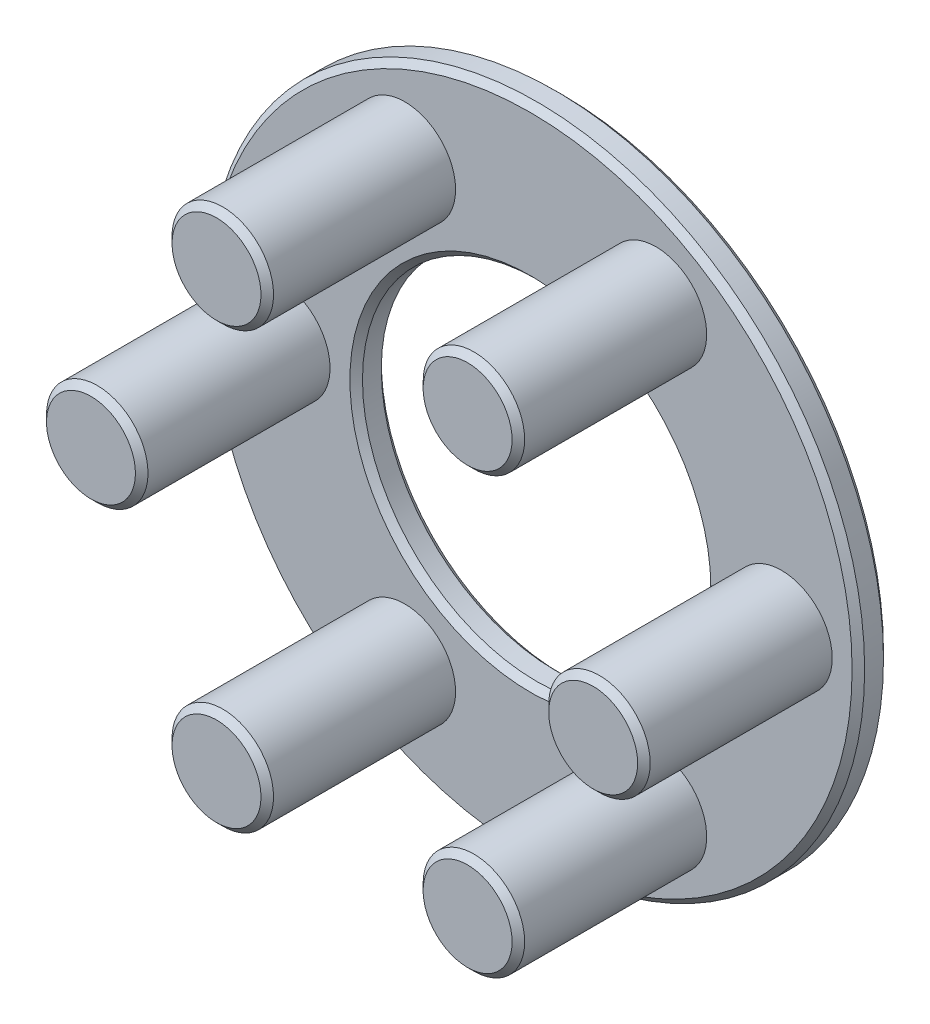
SolidWorks part; units mm, degrees
ref_plane "Front Plane" through (0, 0, 0) normal (0, 0, 1) x (1, 0, 0)
ref_plane "Top Plane" through (0, 0, 0) normal (0, 1, 0) x (1, 0, 0)
ref_plane "Right Plane" through (0, 0, 0) normal (1, 0, 0) x (0, 0, -1)
sketch "Sketch1" plane through (0, 0, 0) normal (0, 0, 1) x (1, 0, 0)
  line L0 (-31.35, 0) -> (-16.65, 0) construction
  circle A0 centre (0, 0) radius 16.65
  circle A1 centre (0, 0) radius 31.35
  circle A2 centre (0, 0) radius 24 construction
  point P7 (-24, 0)
  point P8 (-24, 0)
  point P9 (-6.9637, 0)
  point P10 (-41.0363, 0)
  dimension "D1" = 48
  dimension "D2" = 14.7
extrude "Boss-Extrude1" add sketch "Sketch1" against normal blind 3
sketch "Sketch2" plane through (0, 0, 0) normal (0, 0, 1) x (1, 0, 0)
  line L0 (16.65, 0) -> (31.35, 0) construction
  circle A0 centre (0, 0) radius 16.65 construction
  circle A1 centre (0, 0) radius 31.35 construction
  circle A2 centre (24, 0) radius 4.85
  dimension "D1" = 9.7
extrude "Boss-Extrude2" add sketch "Sketch2" along normal blind 18
pattern_circular "CirPattern1" count 6 over 360 about axis through (0, 0, 0) along (0, 0, 1) of "Boss-Extrude2"
chamfer "Chamfer1" distance 0.6 angle 45 10 edges at (-14.425, -24.9848, 18) (14.425, -24.9848, 18) (28.85, 0, 18) (14.425, 24.9848, 18) (-28.85, 0, 18) (-14.425, 24.9848, 18) (31.35, 0, -3) (31.35, 0, 0) (16.65, 0, -3) (16.65, 0, 0)
